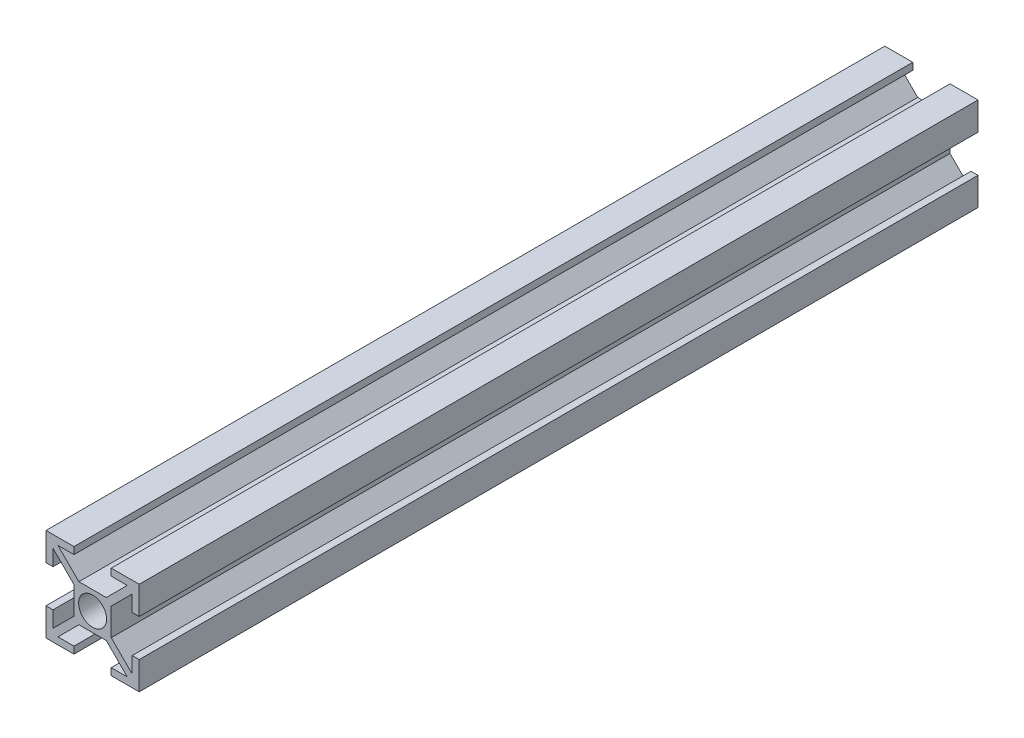
SolidWorks part; units mm, degrees
material "3.0205 (EN-AW 1200)"
ref_plane "Plano frontal" through (0, 0, 0) normal (0, 0, 1) x (1, 0, 0)
ref_plane "Plano superior" through (0, 0, 0) normal (0, 1, 0) x (1, 0, 0)
ref_plane "Plano direito" through (0, 0, 0) normal (1, 0, 0) x (0, 0, -1)
sketch "Esboço1" plane through (0, 0, 0) normal (0, 0, 1) x (1, 0, 0)
  line L0 (-2.9393, 4) -> (2.9393, 4)
  line L1 (-10, -10) -> (-4, -10)
  line L2 (-10, -10) -> (-10, -4)
  line L3 (-10, 10) -> (-4, 10)
  line L4 (10, -10) -> (10, -4)
  line L5 (-10, -10) -> (-4, -4) construction
  line L6 (-10, 10) -> (0, 0) construction
  line L7 (-7.4393, -8.5) -> (-2.9393, -4)
  line L8 (4, -10) -> (10, -10)
  line L9 (-8.5, -7.4393) -> (-4, -2.9393)
  line L10 (-8.5, 7.4393) -> (-4, 2.9393)
  line L11 (-7.4393, -8.5) -> (-4, -8.5)
  line L12 (-8.5, -7.4393) -> (-8.5, -4)
  line L13 (-7.4393, 8.5) -> (-4, 8.5)
  line L14 (8.5, -7.4393) -> (8.5, -4)
  line L17 (-4, 10) -> (-4, 8.5)
  line L18 (4, -8.5) -> (7.4393, -8.5)
  line L19 (-10, -4) -> (-8.5, -4)
  line L20 (4, 10) -> (4, 8.5)
  line L21 (-10, 4) -> (-8.5, 4)
  line L22 (-4, 2.9393) -> (-4, -2.9393)
  line L23 (-4, -8.5) -> (-4, -10)
  line L24 (-8.5, 4) -> (-8.5, 7.4393)
  line L25 (-10, 4) -> (-10, 10)
  line L26 (-7.4393, 8.5) -> (-2.9393, 4)
  line L27 (4, 8.5) -> (7.4393, 8.5)
  line L28 (-2.9393, -4) -> (2.9393, -4)
  line L29 (4, 10) -> (10, 10)
  line L30 (4, -8.5) -> (4, -10)
  line L31 (10, 4) -> (10, 10)
  line L32 (8.5, 4) -> (8.5, 7.4393)
  line L33 (-10.5303, -9.4697) -> (9.4697, 10.5303) construction
  line L34 (8.5, 4) -> (10, 4)
  line L35 (8.5, -4) -> (10, -4)
  line L36 (-10, -10) -> (10, 10) construction
  line L37 (4, 2.9393) -> (4, -2.9393)
  line L38 (-9.4697, -10.5303) -> (10.5303, 9.4697) construction
  line L40 (2.9393, -4) -> (7.4393, -8.5)
  line L41 (4, -4) -> (10, -10) construction
  line L43 (4, -2.9393) -> (8.5, -7.4393)
  line L44 (4, 0) -> (10, 0) construction
  line L45 (4, 2.9393) -> (8.5, 7.4393)
  line L47 (4, 4) -> (10, 10) construction
  line L48 (2.9393, 4) -> (7.4393, 8.5)
  circle A0 centre (0, 0) radius 3
  point P0 (0, 0)
  point P14 (-4.0323, -3.9672)
  dimension "D5" = 6
  dimension "D1" = 0.75
  dimension "D3" = 1.5
  dimension "D4" = 20
  dimension "D6" = 8
  dimension "D7" = 20
  dimension "D9" = 1.5
  dimension "D2" = 8
extrude "Ressalto-extrusão1" add sketch "Esboço1" along normal blind 180
